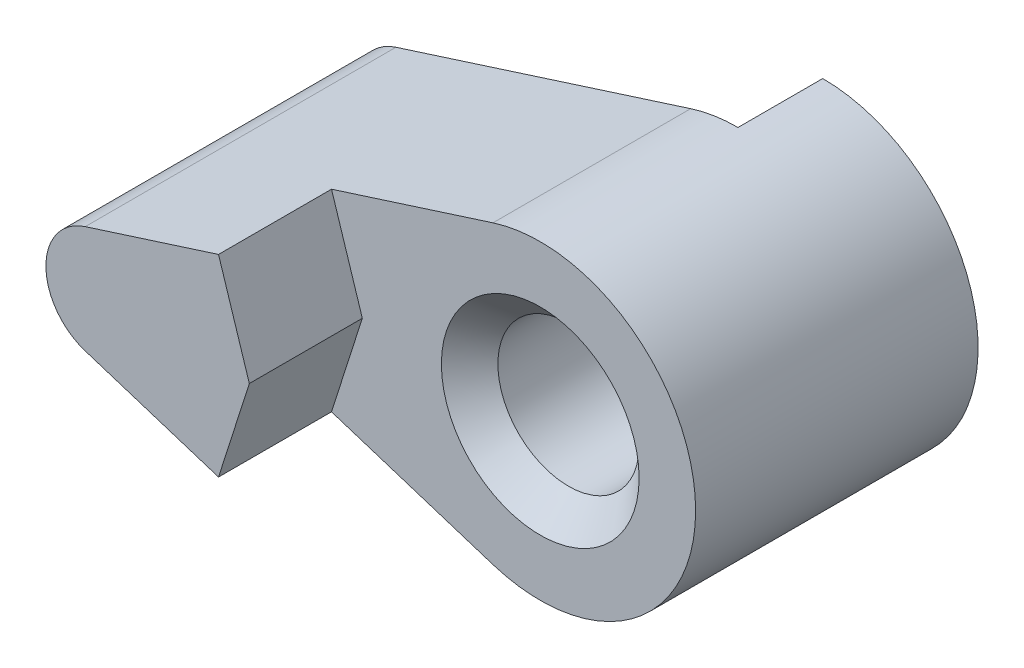
SolidWorks part; units mm, degrees
material "Alliage 7079"
ref_plane "Face" through (0, 0, 0) normal (0, 0, 1) x (1, 0, 0)
ref_plane "Dessus" through (0, 0, 0) normal (0, 1, 0) x (1, 0, 0)
ref_plane "Droite" through (0, 0, 0) normal (1, 0, 0) x (0, 0, -1)
sketch "Esquisse1" plane through (0, 0, 0) normal (0, 0, 1) x (1, 0, 0)
  line L0 (0, 0) -> (-27.4049, 0) construction
  line L1 (-1.6739, 5.2391) -> (-12.1087, 1.9051)
  line L2 (-12.1087, -1.9051) -> (-1.6739, -5.2391)
  line L3 (-13.5, 0) -> (-13.5, 7.9669) construction
  arc A0 (-1.6739, -5.2391) -> (-1.6739, 5.2391) centre (0, 0) ccw
  circle A1 centre (0, 0) radius 2.5
  arc A2 (-12.1087, 1.9051) -> (-12.1087, -1.9051) centre (-11.5, 0) ccw
  point P9 (-18.0714, 0)
  dimension "D1" = 11
  dimension "D3" = 5
  dimension "D4" = 2
  dimension "D2" = 11.5
extrude "Extrusion1" add sketch "Esquisse1" along normal blind 14
sketch "Esquisse2" plane through (0, 0, 14) normal (0, 0, 1) x (1, 0, 0)
  line L0 (-1.6739, 5.2391) -> (-7.3893, 3.413)
  line L1 (-1.6739, 5.2391) -> (-12.1087, 1.9051) construction
  line L2 (-1.6739, -5.2391) -> (-7.3893, -3.413)
  line L3 (-7.3893, 3.413) -> (-6.2988, 0)
  line L4 (-6.2988, 0) -> (-7.3893, -3.413)
  line L6 (0, 0) -> (-13.3545, 0) construction
  arc A0 (-1.6739, -5.2391) -> (-1.6739, 5.2391) centre (0, 0) ccw
  dimension "D1" = 6
  dimension "D2" = 11
extrude "Enlèv. mat.-Extru.1" cut sketch "Esquisse2" against normal blind 4
sketch "Esquisse4" plane through (0, 0, 0) normal (0, 0, -1) x (-1, 0, 0)
  line L0 (1.6739, -5.2391) -> (12.1087, -1.9051)
  line L1 (12.1087, 1.9051) -> (1.6739, 5.2391)
  line L2 (-19, 0) -> (-19, 7.9669) construction
  line L3 (0, 5.5) -> (-1.8811, -5.1683)
  line L4 (0, 0) -> (0, 7.9669) construction
  line L5 (0, 0) -> (0, -8.0447) construction
  arc A0 (-1.8811, -5.1683) -> (1.6739, -5.2391) centre (0, 0) ccw
  circle A1 centre (0, 0) radius 2.5
  arc A2 (12.1087, -1.9051) -> (12.1087, 1.9051) centre (11.5, 0) ccw
  arc A3 (1.6739, 5.2391) -> (0, 5.5) centre (0, 0) ccw
  dimension "D1" = 5
  dimension "D2" = 2
  dimension "D3" = 11.5
  dimension "D4" = 10
extrude "Enlèv. mat.-Extru.2" cut sketch "Esquisse4" against normal blind 3
chamfer "Chanfrein1" distance 1 angle 45 1 edges at (2.5, 0, 10)
